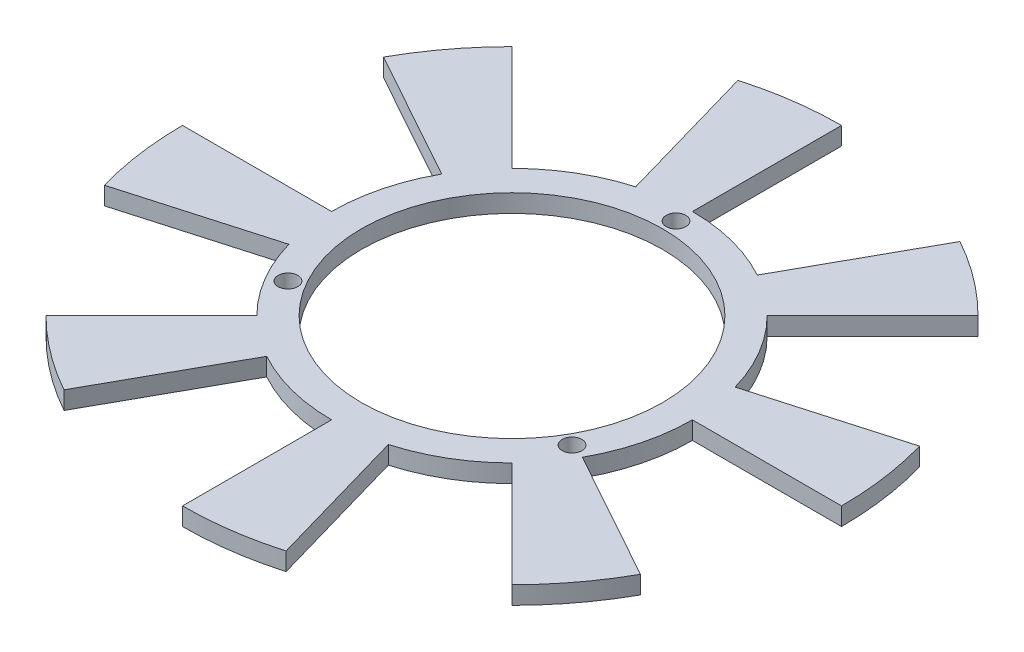
SolidWorks part; units mm, degrees
material "AISI 1010 Steel, hot rolled bar"
ref_plane "Front Plane" through (0, 0, 0) normal (0, 0, 1) x (1, 0, 0)
ref_plane "Top Plane" through (0, 0, 0) normal (0, 1, 0) x (1, 0, 0)
ref_plane "Right Plane" through (0, 0, 0) normal (1, 0, 0) x (0, 0, -1)
sketch "Sketch1" plane through (0, 0, 0) normal (0, 1, 0) x (1, 0, 0)
  circle A0 centre (0, 0) radius 25.25
  dimension "D1" = 50.5
extrude "Extrude-Thin1" add sketch "Sketch1" against normal blind 3 thin
sketch "Sketch2" plane through (0, 0, 0) normal (0, 1, 0) x (1, 0, 0)
  line L0 (0, -30.25) -> (0, 30.25) construction
  line L1 (0, 0) -> (23.8157, -13.75) construction
  line L2 (0, 0) -> (-23.8157, -13.75) construction
  circle A0 centre (0, 27.5) radius 1.65
  circle A1 centre (0, 0) radius 30.25 construction
  circle A4 centre (0, 0) radius 27.5 construction
  circle A7 centre (23.8157, -13.75) radius 1.65
  circle A8 centre (-23.8157, -13.75) radius 1.65
  dimension "D1" = 55
  dimension "D2" = 3.3
  dimension "D3" = 120
  dimension "D4" = 120
extrude "Cut-Extrude3" cut sketch "Sketch2" against normal blind 10
sketch "Sketch5" plane through (0, -3, 0) normal (0, -1, 0) x (1, 0, 0)
  line L0 (0, 0) -> (0, 35.9971) construction
  line L1 (0, 0) -> (9.4011, 32.7855) construction
  line L2 (0, 55.25) -> (0, 30.25)
  line L3 (8.338, 29.0782) -> (15.229, 53.1097)
  line L4 (39.0676, 39.0676) -> (21.39, 21.39)
  line L5 (26.4572, 14.6655) -> (48.3227, 26.7857)
  line L6 (55.25, 0) -> (30.25, 0)
  line L7 (29.0782, -8.338) -> (53.1097, -15.229)
  line L8 (39.0676, -39.0676) -> (21.39, -21.39)
  line L9 (14.6655, -26.4572) -> (26.7857, -48.3227)
  line L10 (0, -55.25) -> (0, -30.25)
  line L11 (-8.338, -29.0782) -> (-15.229, -53.1097)
  line L12 (-39.0676, -39.0676) -> (-21.39, -21.39)
  line L13 (-26.4572, -14.6655) -> (-48.3227, -26.7857)
  line L14 (-55.25, 0) -> (-30.25, 0)
  line L15 (-29.0782, 8.338) -> (-53.1097, 15.229)
  line L16 (-39.0676, 39.0676) -> (-21.39, 21.39)
  line L17 (-14.6655, 26.4572) -> (-26.7857, 48.3227)
  circle A0 centre (0, 0) radius 30.25 construction
  arc A1 (8.338, 29.0782) -> (0, 30.25) centre (0, 0) ccw
  arc A2 (15.229, 53.1097) -> (0, 55.25) centre (0, 0) ccw
  arc A3 (48.3227, 26.7857) -> (39.0676, 39.0676) centre (0, 0) ccw
  arc A4 (26.4572, 14.6655) -> (21.39, 21.39) centre (0, 0) ccw
  arc A5 (53.1097, -15.229) -> (55.25, 0) centre (0, 0) ccw
  arc A6 (29.0782, -8.338) -> (30.25, 0) centre (0, 0) ccw
  arc A7 (26.7857, -48.3227) -> (39.0676, -39.0676) centre (0, 0) ccw
  arc A8 (14.6655, -26.4572) -> (21.39, -21.39) centre (0, 0) ccw
  arc A9 (-15.229, -53.1097) -> (0, -55.25) centre (0, 0) ccw
  arc A10 (-8.338, -29.0782) -> (0, -30.25) centre (0, 0) ccw
  arc A11 (-48.3227, -26.7857) -> (-39.0676, -39.0676) centre (0, 0) ccw
  arc A12 (-26.4572, -14.6655) -> (-21.39, -21.39) centre (0, 0) ccw
  arc A13 (-53.1097, 15.229) -> (-55.25, 0) centre (0, 0) ccw
  arc A14 (-29.0782, 8.338) -> (-30.25, 0) centre (0, 0) ccw
  arc A15 (-26.7857, 48.3227) -> (-39.0676, 39.0676) centre (0, 0) ccw
  arc A16 (-14.6655, 26.4572) -> (-21.39, 21.39) centre (0, 0) ccw
  point P87 (0, 0)
  dimension "D2" = 25
  dimension "D1" = 16
  dimension "D3" = 8
extrude "Boss-Extrude1" add sketch "Sketch5" against normal blind 3
